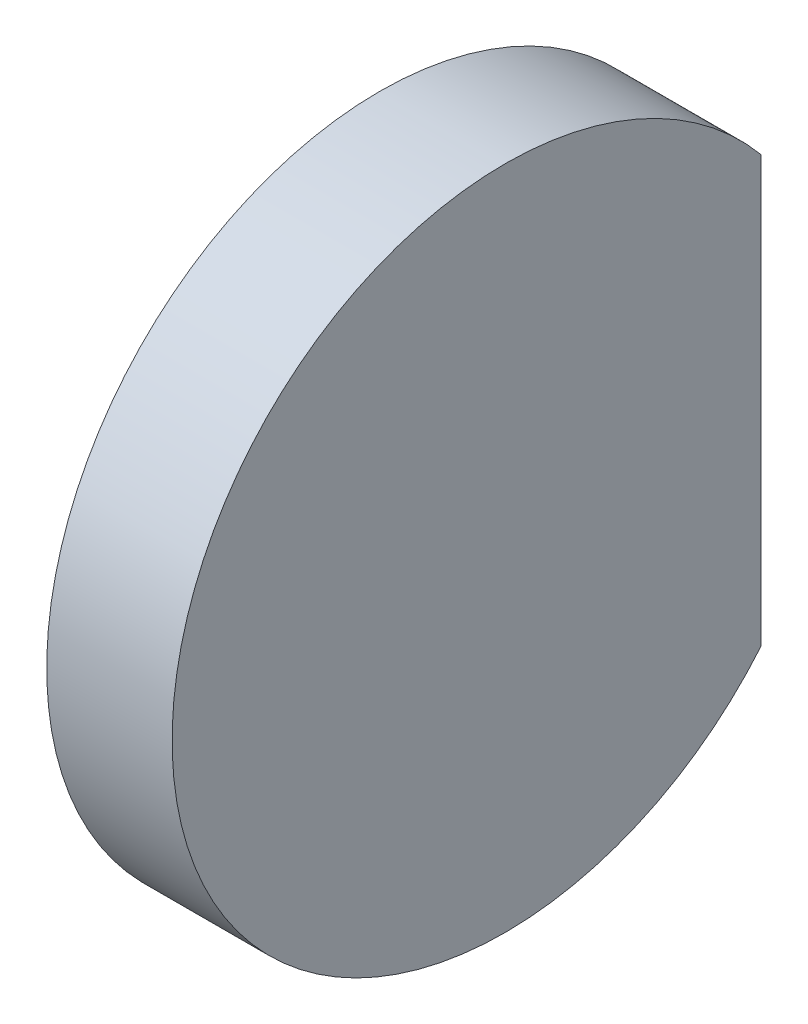
SolidWorks part; units mm, degrees
material "Стекло"
ref_plane "Front" through (0, 0, 0) normal (0, 0, 1) x (1, 0, 0)
ref_plane "Top" through (0, 0, 0) normal (0, 1, 0) x (1, 0, 0)
ref_plane "Right" through (0, 0, 0) normal (1, 0, 0) x (0, 0, -1)
sketch "Эскиз1" plane through (0, 0, 0) normal (0, 0, 1) x (1, 0, 0)
  line L0 (0, 0) -> (0, 16.6394) construction
  line L1 (0.5519, 6.5) -> (3, 6.5)
  line L2 (3, 6.5) -> (3, 0)
  line L3 (3, 0) -> (0, 0)
  line L4 (0, 0) -> (12.8532, 0) construction
  arc A0 (0, 0) -> (0.5519, 6.5) centre (38.55, 0) cw
  dimension "D1" = 38.55
  dimension "D2" = 13
  dimension "D3" = 3
revolve "Повернуть1" add sketch "Эскиз1" angle 360 about L4
sketch "Эскиз2" plane through (3, 0, 0) normal (1, 0, 0) x (0, 0, -1)
  line L0 (5, 4.1533) -> (5, -4.1533)
  line L1 (-6.5, 0) -> (-6.5, 10.4831) construction
  circle A0 centre (0, 0) radius 6.5 construction
  circle M1 centre (0, 0) radius 6.5
  dimension "D1" = 11.5
extrude "Вырез-Вытянуть1" cut sketch "Эскиз2" against normal through all contours L0 M1
